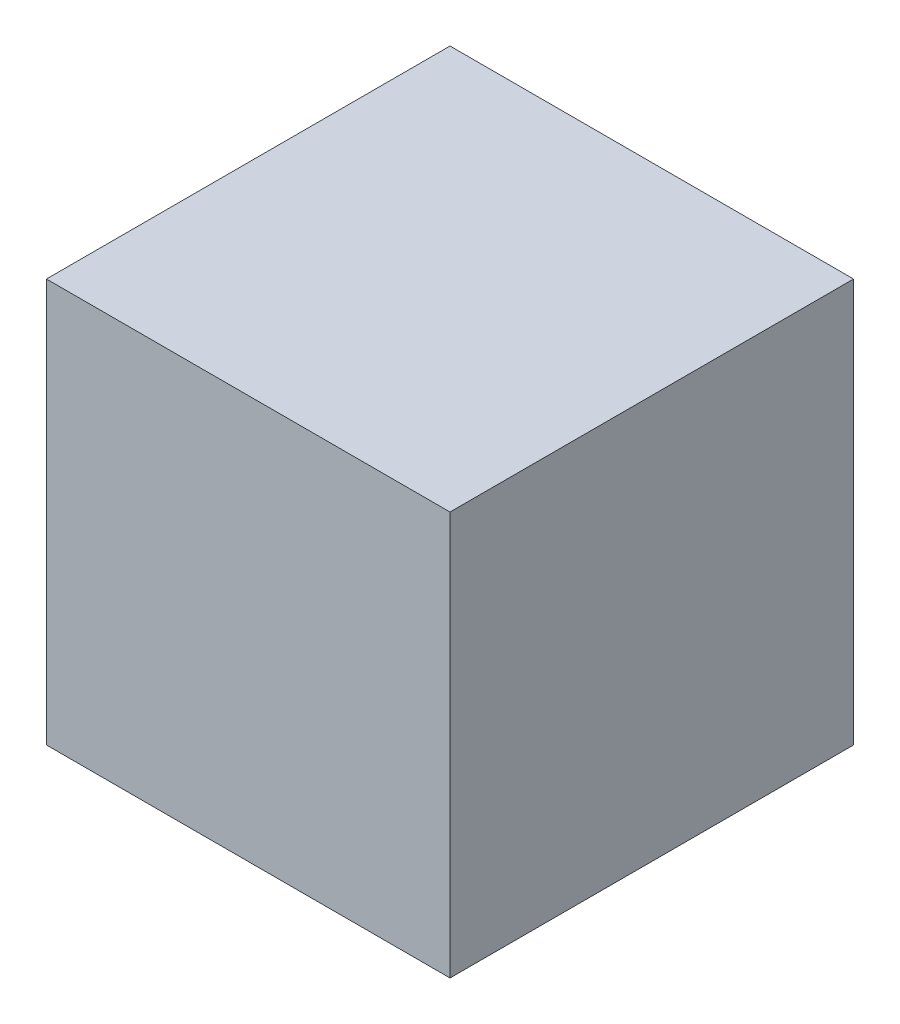
SolidWorks part; units mm, degrees
ref_plane "Front Plane" through (0, 0, 0) normal (0, 0, 1) x (1, 0, 0)
ref_plane "Top Plane" through (0, 0, 0) normal (0, 1, 0) x (1, 0, 0)
ref_plane "Right Plane" through (0, 0, 0) normal (1, 0, 0) x (0, 0, -1)
sketch "Sketch2" plane through (0, 0, 0) normal (0, 0, 1) x (1, 0, 0)
  line L1 (-20, 20) -> (20, 20)
  line L2 (-20, 20) -> (-20, -20)
  line L3 (-20, -20) -> (20, -20)
  line L4 (20, 20) -> (20, -20)
  line L5 (-20, 20) -> (20, -20) construction
  line L6 (-20, -20) -> (20, 20) construction
  point P0 (0, 0)
  dimension "D1" = 40
  dimension "D2" = 40
extrude "Boss-Extrude1" add sketch "Sketch2" along normal blind 40
